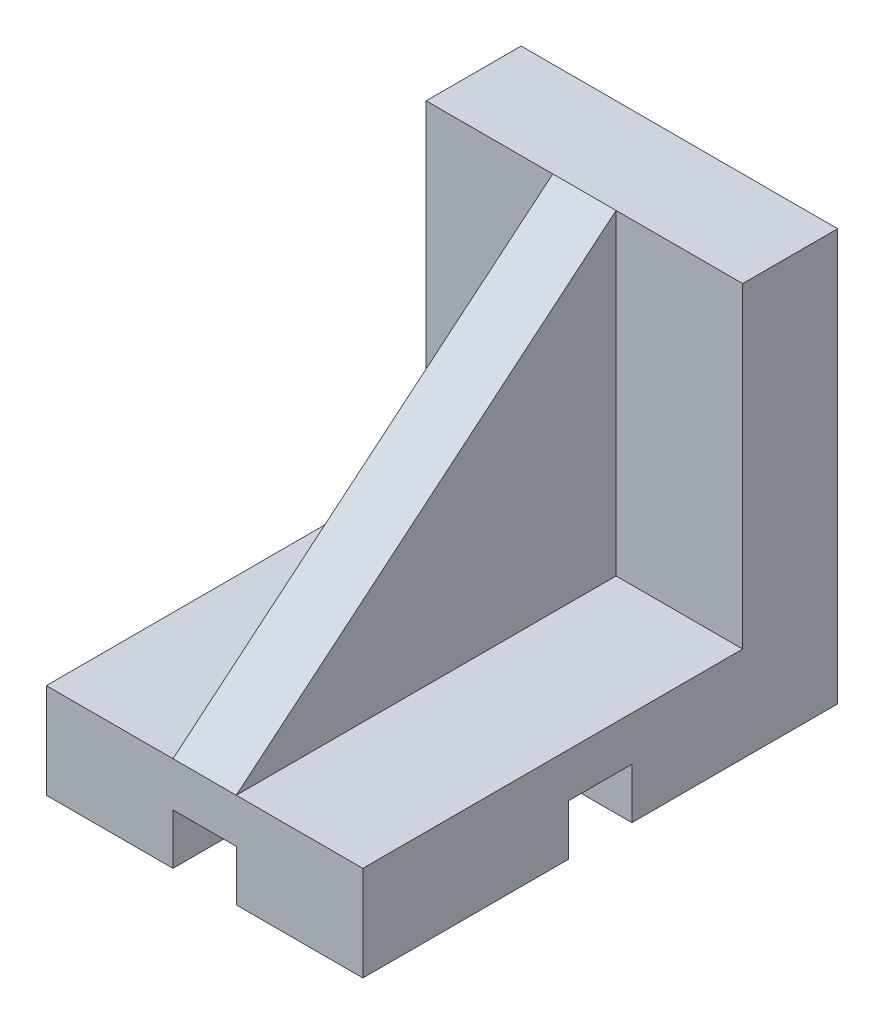
SolidWorks part; units mm, degrees
ref_plane "Ön Düzlem" through (0, 0, 0) normal (0, 0, 1) x (1, 0, 0)
ref_plane "Üst Düzlem" through (0, 0, 0) normal (0, 1, 0) x (1, 0, 0)
ref_plane "Sağ Düzlem" through (0, 0, 0) normal (1, 0, 0) x (0, 0, -1)
sketch "Çizim1" plane through (0, 0, 0) normal (0, 1, 0) x (1, 0, 0)
  line L1 (-25, 37.5) -> (25, 37.5)
  line L2 (-25, 37.5) -> (-25, -37.5)
  line L3 (-25, -37.5) -> (25, -37.5)
  line L4 (25, 37.5) -> (25, -37.5)
  line L5 (-25, 37.5) -> (25, -37.5) construction
  line L6 (-25, -37.5) -> (25, 37.5) construction
  point P0 (0, 0)
  dimension "D1" = 75
  dimension "D2" = 50
extrude "Yükseklik-Ekstrüzyon1" add sketch "Çizim1" along normal blind 15
sketch "Çizim2" plane through (0, 15, 0) normal (0, 1, 0) x (1, 0, 0)
  line L0 (25, -37.5) -> (25, 37.5) construction
  line L1 (-25, 37.5) -> (25, 37.5)
  line L2 (-25, 37.5) -> (-25, 22.5)
  line L3 (-25, 22.5) -> (25, 22.5)
  line L4 (25, 37.5) -> (25, 22.5)
  dimension "D1" = 15
extrude "Yükseklik-Ekstrüzyon2" add sketch "Çizim2" along normal blind 50
sketch "Çizim4" plane through (0, 0, 0) normal (1, 0, 0) x (0, 0, -1)
  line L0 (22.5, 65) -> (-37.5, 15)
  line L1 (-37.5, 15) -> (22.5, 15)
  line L2 (22.5, 15) -> (22.5, 65)
extrude "Yükseklik-Ekstrüzyon3" add sketch "Çizim4" along normal mid plane 10
sketch "Çizim5" plane through (0, 0, 37.5) normal (0, 0, 1) x (1, 0, 0)
  line L0 (-25, 0) -> (25, 0) construction
  line L1 (-5, 0) -> (5, 0)
  line L2 (-5, 0) -> (-5, 8)
  line L3 (-5, 8) -> (5, 8)
  line L4 (5, 0) -> (5, 8)
  line L5 (-5, 65) -> (-5, 15) construction
  line L6 (5, 65) -> (5, 15) construction
  dimension "D1" = 8
extrude "Kes-Ekstrüzyon1" cut sketch "Çizim5" against normal through all
sketch "Çizim6" plane through (25, 0, 0) normal (1, 0, 0) x (0, 0, -1)
  line L0 (-37.5, 0) -> (37.5, 0) construction
  line L1 (-5, 0) -> (5, 0)
  line L2 (-5, 0) -> (-5, 8)
  line L3 (-5, 8) -> (5, 8)
  line L4 (5, 0) -> (5, 8)
  dimension "D1" = 8
  dimension "D2" = 10
  dimension "D3" = 32.5
extrude "Kes-Ekstrüzyon2" cut sketch "Çizim6" against normal through all
